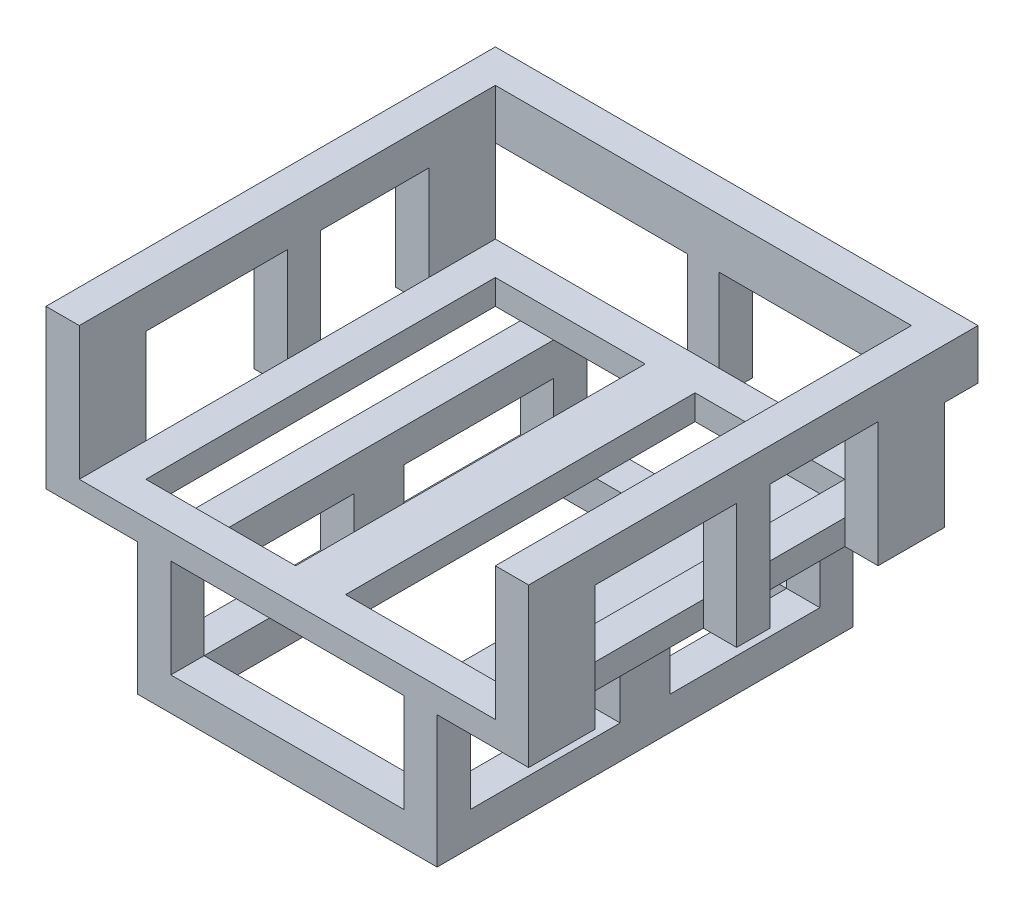
SolidWorks part; units mm, degrees
ref_plane "Front Plane" through (0, 0, 0) normal (0, 0, 1) x (1, 0, 0)
ref_plane "Top Plane" through (0, 0, 0) normal (0, 1, 0) x (1, 0, 0)
ref_plane "Right Plane" through (0, 0, 0) normal (1, 0, 0) x (0, 0, -1)
sketch "Sketch1" plane through (0, 0, 0) normal (0, 1, 0) x (1, 0, 0)
  line L0 (-1.5, 9.5) -> (-1.5, -11.5)
  line L1 (-12.5, 11.5) -> (12.5, 11.5)
  line L2 (-12.5, 11.5) -> (-12.5, -13.5)
  line L3 (-12.5, -13.5) -> (12.5, -13.5)
  line L4 (12.5, 11.5) -> (12.5, -13.5)
  line L5 (-10.5, 9.5) -> (-1.5, 9.5)
  line L6 (-10.5, 9.5) -> (-10.5, -11.5)
  line L7 (-10.5, -11.5) -> (-1.5, -11.5)
  line L8 (10.5, 9.5) -> (10.5, -11.5)
  line L10 (1.5, -11.5) -> (1.5, 9.5)
  line L11 (1.5, -11.5) -> (10.5, -11.5)
  line L12 (1.5, 9.5) -> (10.5, 9.5)
  dimension "D1" = 25
  dimension "D2" = 25
  dimension "D3" = 12.5
  dimension "D4" = 11.5
  dimension "D5" = 2
  dimension "D6" = 2
  dimension "D7" = 2
  dimension "D8" = 1.5
  dimension "D9" = 1.5
  dimension "D10" = 2
extrude "Boss-Extrude1" add sketch "Sketch1" along normal blind 1.5
ref_plane "Plane1" through (12.5, 0, 0) normal (1, 0, 0) x (0, 0, -1)
sketch "Sketch2" plane through (12.5, 0, 0) normal (1, 0, 0) x (0, 0, -1)
  line L0 (-1, 7.5) -> (-1, 0)
  line L1 (-9.5, 0) -> (-1, 0)
  line L2 (-13.5, 0) -> (-13.5, 9.5)
  line L3 (-13.5, 9.5) -> (11.5, 9.5)
  line L4 (11.5, 0) -> (11.5, 9.5)
  line L5 (-9.5, 7.5) -> (-1, 7.5)
  line L6 (-9.5, 7.5) -> (-9.5, 0)
  line L7 (-9.5, 0) -> (7.5, 0)
  line L8 (7.5, 7.5) -> (7.5, 0)
  line L9 (1, 7.5) -> (1, 0)
  line L10 (1, 7.5) -> (7.5, 7.5)
  line L20 (1, 0) -> (7.5, 0)
  line L21 (-13.5, 0) -> (-9.5, 0)
  line L22 (-1, 0) -> (1, 0)
  line L23 (7.5, 0) -> (11.5, 0)
  point P9 (0, 7.5)
  dimension "D1" = 9.5
  dimension "D2" = 25
  dimension "D3" = 2
  dimension "D6" = 1
  dimension "D7" = 1
extrude "Boss-Extrude2" add sketch "Sketch2" along normal blind 2 contours L5 L8 L1 L4 L3 L2 L6
ref_plane "Plane2" through (-12.5, 0, 0) normal (-1, 0, 0) x (0, 0, 1)
sketch "Sketch3" plane through (-12.5, 0, 0) normal (-1, 0, 0) x (0, 0, 1)
  line L0 (1, 7.2) -> (1, 0)
  line L1 (-7.5, 0) -> (-1, 0)
  line L2 (-11.5, 0) -> (-11.5, 9.5)
  line L3 (-11.5, 9.5) -> (13.5, 9.5)
  line L4 (13.5, 0) -> (13.5, 9.5)
  line L5 (-7.5, 7.2) -> (-1, 7.2)
  line L6 (-7.5, 7.2) -> (-7.5, 0)
  line L7 (-7.5, 0) -> (-1, 0)
  line L8 (9.5, 7.2) -> (9.5, 0)
  line L9 (-1, 7.2) -> (-1, 0)
  line L10 (-1, 0) -> (1, 0)
  line L11 (1, 7.2) -> (9.5, 7.2)
  line L21 (1, 0) -> (9.5, 0)
  line L22 (1, 0) -> (9.5, 0)
  line L23 (13.5, 0) -> (9.5, 0)
  line L24 (9.5, 0) -> (9.6291, 0.0055)
  line L25 (1, 0) -> (-1, 0)
  line L26 (-7.5, 0) -> (-11.5, 0)
  point P13 (0, 7.2)
  dimension "D1" = 25
  dimension "D2" = 9.5
  dimension "D3" = 7.2
  dimension "D4" = 4
  dimension "D5" = 4
  dimension "D6" = 1
  dimension "D7" = 1
extrude "Boss-Extrude3" add sketch "Sketch3" along normal blind 2 contours L5 L8 L1 L4 L3 L2 L6
ref_plane "Plane6" through (0, 0, -11.5) normal (0, 0, -1) x (-1, 0, 0)
sketch "Sketch10" plane through (0, 0, -11.5) normal (0, 0, -1) x (-1, 0, 0)
  line L0 (-14.5, 0) -> (-14.5, 9.5) construction
  line L1 (14.5, 9.5) -> (-14.5, 9.5)
  line L2 (14.5, 9.5) -> (14.5, 6.5)
  line L3 (14.5, 6.5) -> (0.95, 6.5)
  line L4 (-14.5, 9.5) -> (-14.5, 6.5)
  line L5 (-0.948, 6.5) -> (-14.5, 6.5)
  line L6 (-0.948, 0) -> (0.95, 0)
  line L7 (-0.948, 6.5) -> (-0.948, 0)
  line L8 (-12.5, 1.5) -> (-12.5, 9.5) construction
  line L9 (0.95, 6.5) -> (0.95, 0)
  line L10 (12.5, 1.5) -> (12.5, 9.5) construction
  dimension "D1" = 11.552
  dimension "D2" = 11.55
extrude "Boss-Extrude8" add sketch "Sketch10" along normal blind 2
ref_plane "Plane9" through (0, 0, 0) normal (0, -1, 0) x (-1, 0, 0)
sketch "Sketch12" plane through (0, 0, 0) normal (0, -1, 0) x (-1, 0, 0)
  line L3 (-14.5, 11.5) -> (-0.948, 11.5) construction
  line L4 (14.5, -13.5) -> (-14.5, -13.5) construction
  line L5 (-7, 11.5) -> (-9, 11.5)
  line L6 (-7, 11.5) -> (-7, -13.5)
  line L7 (-7, -13.5) -> (-9, -13.5)
  line L8 (-9, 11.5) -> (-9, -13.5)
  line L9 (0.95, 11.5) -> (14.5, 11.5) construction
  line L10 (7, -13.5) -> (9, -13.5)
  line L11 (7, -13.5) -> (7, 11.5)
  line L12 (7, 11.5) -> (9, 11.5)
  line L13 (9, -13.5) -> (9, 11.5)
  point P6 (7, 0)
  point P7 (-7, 0)
  dimension "D1" = 2
  dimension "D2" = 7
  dimension "D3" = 7
  dimension "D4" = 2
extrude "Boss-Extrude10" add sketch "Sketch12" along normal blind 5.93
ref_plane "Plane8" through (0, -5.93, 0) normal (0, -1, 0) x (-1, 0, 0)
sketch "Sketch11" plane through (0, -5.93, 0) normal (0, -1, 0) x (-1, 0, 0)
  line L1 (9, -13.5) -> (-9, -13.5)
  line L2 (9, -13.5) -> (9, 11.5)
  line L3 (9, 11.5) -> (-9, 11.5)
  line L4 (-9, -13.5) -> (-9, 11.5)
  line L5 (-7, 9.5) -> (7, 9.5)
  line L6 (-7, 9.5) -> (-7, -11.5)
  line L7 (-7, -11.5) -> (7, -11.5)
  line L8 (7, 9.5) -> (7, -11.5)
  point P10 (0, 0)
  dimension "D1" = 7
  dimension "D2" = 7
  dimension "D3" = 2
  dimension "D4" = 2
extrude "Boss-Extrude11" add sketch "Sketch11" along normal blind 2
ref_plane "Plane10" through (-9, 0, 0) normal (-1, 0, 0) x (0, 0, 1)
sketch "Sketch13" plane through (-9, 0, 0) normal (-1, 0, 0) x (0, 0, 1)
  line L0 (13.5, -7.93) -> (-11.5, -7.93) construction
  line L1 (11.5, -2) -> (-9.5, -2)
  line L2 (11.5, -2) -> (11.5, -5.93)
  line L3 (11.5, -5.93) -> (-9.5, -5.93)
  line L4 (-9.5, -2) -> (-9.5, -5.93)
  line L5 (11.5, 0) -> (-9.5, 0) construction
  line L6 (-11.5, -7.93) -> (-11.5, 0) construction
  line L7 (13.5, -7.93) -> (13.5, 0) construction
  line L9 (2.5, -5.93) -> (-0.5, -5.93)
  line L10 (2.5, -5.93) -> (2.5, -2)
  line L11 (2.5, -2) -> (-0.5, -2)
  line L12 (-0.5, -5.93) -> (-0.5, -2)
  dimension "D1" = 2
  dimension "D2" = 2
  dimension "D3" = 2
  dimension "D4" = 2
  dimension "D5" = 9
  dimension "D6" = 9
extrude "Cut-Extrude2" cut sketch "Sketch13" against normal through all contours L3 L12 L1 L4 | L10 L3 L2 L1
